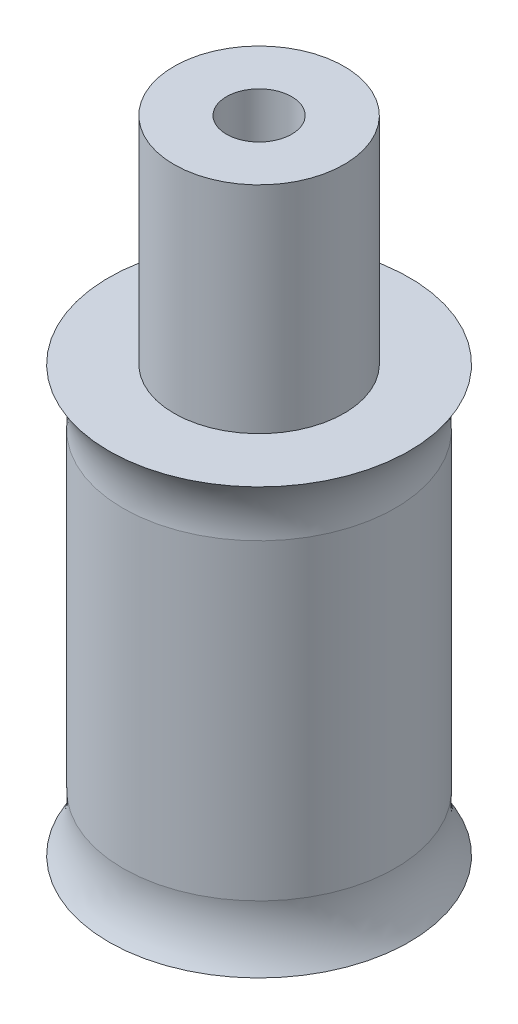
SolidWorks part; units mm, degrees
ref_plane "Alzado" through (0, 0, 0) normal (0, 0, 1) x (1, 0, 0)
ref_plane "Planta" through (0, 0, 0) normal (0, 1, 0) x (1, 0, 0)
ref_plane "Vista lateral" through (0, 0, 0) normal (1, 0, 0) x (0, 0, -1)
ref_axis "Eje1" through (0, 55, 0) along (0, -1, 0)
sketch "Croquis1" plane through (0, 0, 0) normal (0, 0, 1) x (1, 0, 0)
  line L0 (4.8, 15) -> (3, 15)
  line L2 (3, 15) -> (3, 22.6)
  line L3 (4.8, 0) -> (0, 0)
  line L6 (4.8, 0) -> (4.8, 15)
  line L7 (0, 55) -> (0, -55) construction
  line L8 (0, 0) -> (0, 22.6)
  line L9 (3, 22.6) -> (0, 22.6)
  dimension "D1" = 7.6
  dimension "D2" = 15
  dimension "D5" = 3
  dimension "D6" = 4.8
  dimension "D7" = 0
revolve "Revolución2" add sketch "Croquis1" angle 360 about axis through (0, 55, 0) along (0, -1, 0)
sketch "Croquis7" plane through (0, 15, 0) normal (0, 1, 0) x (1, 0, 0)
  circle A0 centre (0, 0) radius 5.3
  circle A1 centre (0, 0) radius 4.8 construction
  dimension "D1" = 0.5
extrude "Saliente-Extruir1" add sketch "Croquis7" against normal blind 2
sketch "Croquis3" plane through (0, 15, 0) normal (0, 1, 0) x (1, 0, 0)
  circle A0 centre (0, 0) radius 1.15
  dimension "D1" = 2.3
extrude "Cortar-Extruir1" cut sketch "Croquis3" against normal blind 7.8 from surface at 7.6 starting at face at (0, 22.6, 3)
sketch "Croquis8" plane through (0, 0, 0) normal (1, 0, 0) x (0, 0, -1)
  line L1 (-5.3, 13) -> (5.3, 13) construction
  line L2 (4.8, 0) -> (4.8, 13) construction
  line L4 (5.3, 15) -> (5.3, 13)
  line L5 (5.3, 13) -> (4.8, 13)
  arc A0 (5.3, 15) -> (4.8, 13) centre (7.7832, 13.3167) ccw
  dimension "D1" = 3
revolve "Cortar-Revolución2" cut sketch "Croquis8" angle 360 about axis through (0, 55, 0) along (0, -1, 0)
ref_plane "Plano1" [suppressed] through (0, 7.5, 0) normal (0, -1, 0) x (-1, 0, 0)
mirror "Simetría1" about plane through (0, 7.5, 0) normal (0, -1, 0) of "Cortar-Revolución2", "Saliente-Extruir1"
sketch "Croquis4" plane through (0, 0, 0) normal (0, -1, 0) x (1, 0, 0)
  circle A0 centre (0, 0) radius 2
  circle A1 centre (0, 0) radius 4.8 construction
  dimension "D1" = 4
extrude "Cortar-Extruir2" cut sketch "Croquis4" against normal blind 2.6
sketch "Croquis9" plane through (0, 0, 0) normal (0, -1, 0) x (1, 0, 0)
  line L0 (-0.4, 3.2) -> (0, 4)
  line L1 (-0.4, 2.4) -> (0.4, 2.4)
  line L2 (-0.4, 2.4) -> (-0.4, 3.2)
  line L4 (0.4, 2.4) -> (0.4, 3.2)
  line L5 (0, 4) -> (0.4, 3.2)
  point P4 (0, 2.4)
  dimension "D1" = 2.4
  dimension "D2" = 0.8
  dimension "D3" = 0.8
  dimension "D4" = 0.8
  dimension "D5" = 1.6
extrude "Cortar-Extruir4" cut sketch "Croquis9" against normal blind 2
